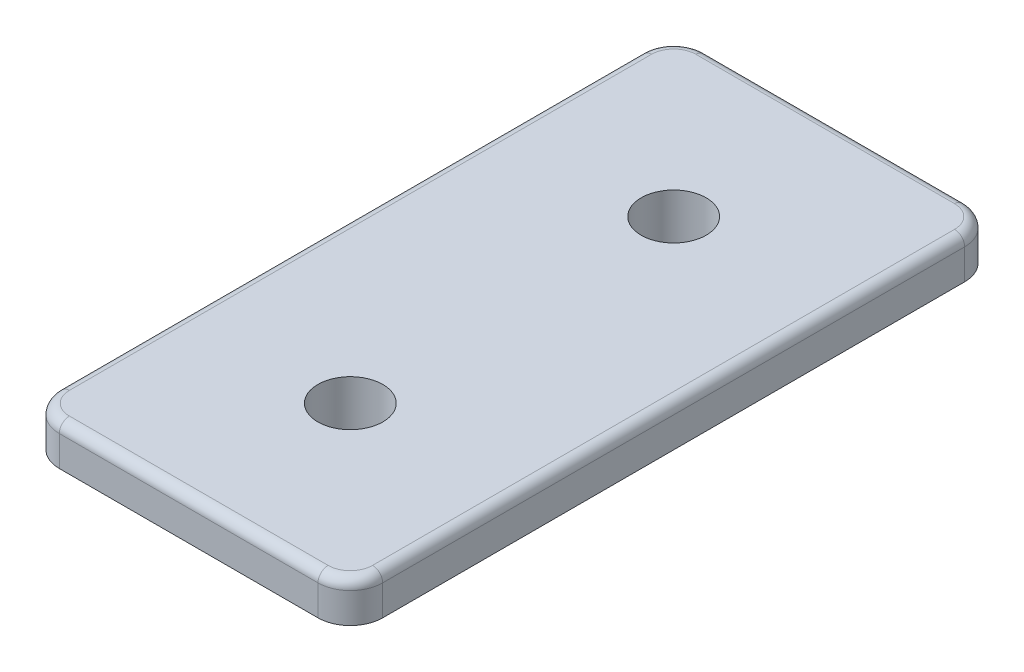
SolidWorks part; units mm, degrees
material "PET"
ref_plane "Front Plane" through (0, 0, 0) normal (0, 0, 1) x (1, 0, 0)
ref_plane "Top Plane" through (0, 0, 0) normal (0, 1, 0) x (1, 0, 0)
ref_plane "Right Plane" through (0, 0, 0) normal (1, 0, 0) x (0, 0, -1)
sketch "Sketch1" plane through (0, 0, 0) normal (0, 1, 0) x (1, 0, 0)
  line L0 (-11.1125, 23.8125) -> (11.1125, 23.8125)
  line L1 (-12.7, -25.4) -> (12.7, -25.4)
  line L2 (-12.7, -25.4) -> (-12.7, 25.4)
  line L3 (-12.7, 25.4) -> (12.7, 25.4)
  line L4 (12.7, -25.4) -> (12.7, 25.4)
  line L5 (-12.7, -25.4) -> (12.7, 25.4) construction
  line L6 (-12.7, 25.4) -> (12.7, -25.4) construction
  line L7 (11.1125, -23.8125) -> (11.1125, 23.8125)
  line L8 (-11.1125, -23.8125) -> (11.1125, -23.8125)
  line L9 (-11.1125, -23.8125) -> (-11.1125, 23.8125)
  line L10 (-10.8585, 23.5585) -> (10.8585, 23.5585)
  line L11 (10.8585, -23.5585) -> (10.8585, 23.5585)
  line L12 (-10.8585, -23.5585) -> (10.8585, -23.5585)
  line L13 (-10.8585, -23.5585) -> (-10.8585, 23.5585)
  point P0 (0, 0)
  dimension "D1" = 50.8
  dimension "D2" = 25.4
  dimension "D3" = 1.5875
  dimension "D4" = 0.254
extrude "Boss-Extrude1" add sketch "Sketch1" along normal blind 0.762 contours L13 L12 L11 L10
sketch "Sketch2" plane through (0, 0.762, 0) normal (0, 1, 0) x (1, 0, 0)
  line L1 (-12.7, -25.4) -> (12.7, -25.4)
  line L2 (-12.7, -25.4) -> (-12.7, 25.4)
  line L3 (-12.7, 25.4) -> (12.7, 25.4)
  line L4 (12.7, -25.4) -> (12.7, 25.4)
  line L5 (-12.7, -25.4) -> (12.7, 25.4) construction
  line L6 (-12.7, 25.4) -> (12.7, -25.4) construction
  point P0 (0, 0)
  dimension "D1" = 25.4
  dimension "D2" = 50.8
extrude "Boss-Extrude2" add sketch "Sketch2" along normal blind 3.175
sketch "Sketch3" plane through (0, 3.937, 0) normal (0, 1, 0) x (1, 0, 0)
  line L0 (-12.7, 25.4) -> (-12.7, -25.4) construction
  line L1 (-12.7, 0) -> (12.7, 0) construction
  line L2 (12.7, -25.4) -> (12.7, 25.4) construction
  circle A0 centre (0, 12.7) radius 2.5527
  circle A1 centre (0, -12.7) radius 2.5527
  dimension "D1" = 5.1054
  dimension "D2" = 12.7
  dimension "D3" = 12.7
extrude "Cut-Extrude1" cut sketch "Sketch3" against normal through all
fillet "Fillet1" radius 2.54 8 edges at (-10.8585, 0.381, 23.5585) (10.8585, 0.381, 23.5585) (-10.8585, 0.381, -23.5585) (10.8585, 0.381, -23.5585) (12.7, 2.3495, -25.4) (12.7, 2.3495, 25.4) (-12.7, 2.3495, -25.4) (-12.7, 2.3495, 25.4)
fillet "Fillet3" radius 0.7937 8 edges at (-11.9561, 3.937, -24.6561) (0, 3.937, -25.4) (11.9561, 3.937, -24.6561) (12.7, 3.937, 0) (11.9561, 3.937, 24.6561) (0, 3.937, 25.4) (-11.9561, 3.937, 24.6561) (-12.7, 3.937, 0)
